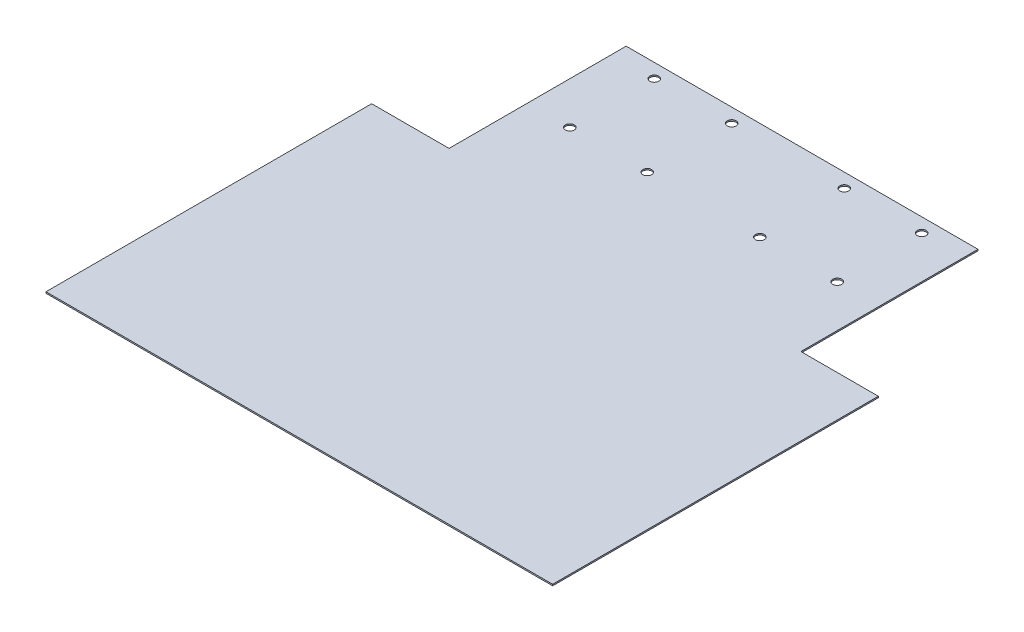
SolidWorks part; units mm, degrees
ref_plane "Alzado" through (0, 0, 0) normal (0, 0, 1) x (1, 0, 0)
ref_plane "Planta" through (0, 0, 0) normal (0, 1, 0) x (1, 0, 0)
ref_plane "Vista lateral" through (0, 0, 0) normal (1, 0, 0) x (0, 0, -1)
sketch "Croquis2" plane through (0, 0, 0) normal (0, 1, 0) x (1, 0, 0)
  line L0 (-90, 26.39) -> (-62.5, 26.39)
  line L1 (90, -89.31) -> (-90, -89.31)
  line L2 (90, -89.31) -> (90, 26.39)
  line L3 (62.5, 89.31) -> (-62.5, 89.31)
  line L4 (-90, -89.31) -> (-90, 26.39)
  line L5 (90, -89.31) -> (-62.5, 62.0208) construction
  line L6 (62.5, 62.0208) -> (-90, -89.31) construction
  line L7 (-62.5, 26.39) -> (-62.5, 89.31)
  line L8 (0, 0) -> (0, 89.31) construction
  line L9 (90, 26.39) -> (62.5, 26.39)
  line L10 (62.5, 26.39) -> (62.5, 89.31)
  point P0 (0, 0)
  dimension "D1" = 125
  dimension "D2" = 180
  dimension "D4" = 62.92
extrude "Saliente-Extruir1" add sketch "Croquis2" along normal blind 0.5
sketch "Croquis3" plane through (90, 0, 0) normal (1, 0, 0) x (0, 0, -1)
  line L0 (-89.31, 0) -> (-87.9363, 0.5)
  line L1 (-89.31, 0.5) -> (26.39, 0.5) construction
  line L2 (-87.9363, 0.5) -> (-89.31, 0.5)
  line L3 (-89.31, 0.5) -> (-89.31, 0)
  dimension "D1" = 70
extrude "Cortar-Extruir1" cut sketch "Croquis3" against normal up to next
sketch "Croquis5" plane through (0, 0.5, 0) normal (0, 1, 0) x (1, 0, 0)
  circle A0 centre (74, -24.975) radius 1.585
extrude "Cortar-Extruir3" cut sketch "Croquis5" against normal up to next (0.5 mm away)
mirror "Simetría1" about plane through (0, 0, 0) normal (1, 0, 0) of "Cortar-Extruir3"
sketch "Croquis6" plane through (0, 0.5, 0) normal (0, 1, 0) x (1, 0, 0)
  circle A0 centre (-56.5, 35.81) radius 1.585
  circle A1 centre (-15.5, 35.81) radius 1.585
  circle A2 centre (-15.5, 84.31) radius 1.585
  circle A3 centre (-56.5, 84.31) radius 1.585
extrude "Cortar-Extruir4" cut sketch "Croquis6" against normal up to next
sketch "Croquis7" plane through (0, 0.5, 0) normal (0, 1, 0) x (1, 0, 0)
  circle A0 centre (56.5, 35.81) radius 1.585
  circle A1 centre (15.5, 35.81) radius 1.585
  circle A2 centre (15.5, 84.31) radius 1.585
  circle A3 centre (56.5, 84.31) radius 1.585
extrude "Cortar-Extruir5" cut sketch "Croquis7" against normal up to next
mirror "Simetría3" about plane through (0, 0, 0) normal (1, 0, 0) of "Saliente-Extruir1"
sketch "Croquis8" plane through (0, 0.5, 0) normal (0, 1, 0) x (1, 0, 0)
  circle A0 centre (-20, 54.31) radius 1.585
  circle A1 centre (-47.5, 54.31) radius 1.585
  circle A2 centre (-47.5, 84.31) radius 1.585
  circle A3 centre (-20, 84.31) radius 1.585
extrude "Cortar-Extruir6" cut sketch "Croquis8" against normal up to next (0.5 mm away)
mirror "Simetría4" about plane through (0, 0, 0) normal (1, 0, 0) of "Cortar-Extruir6"
